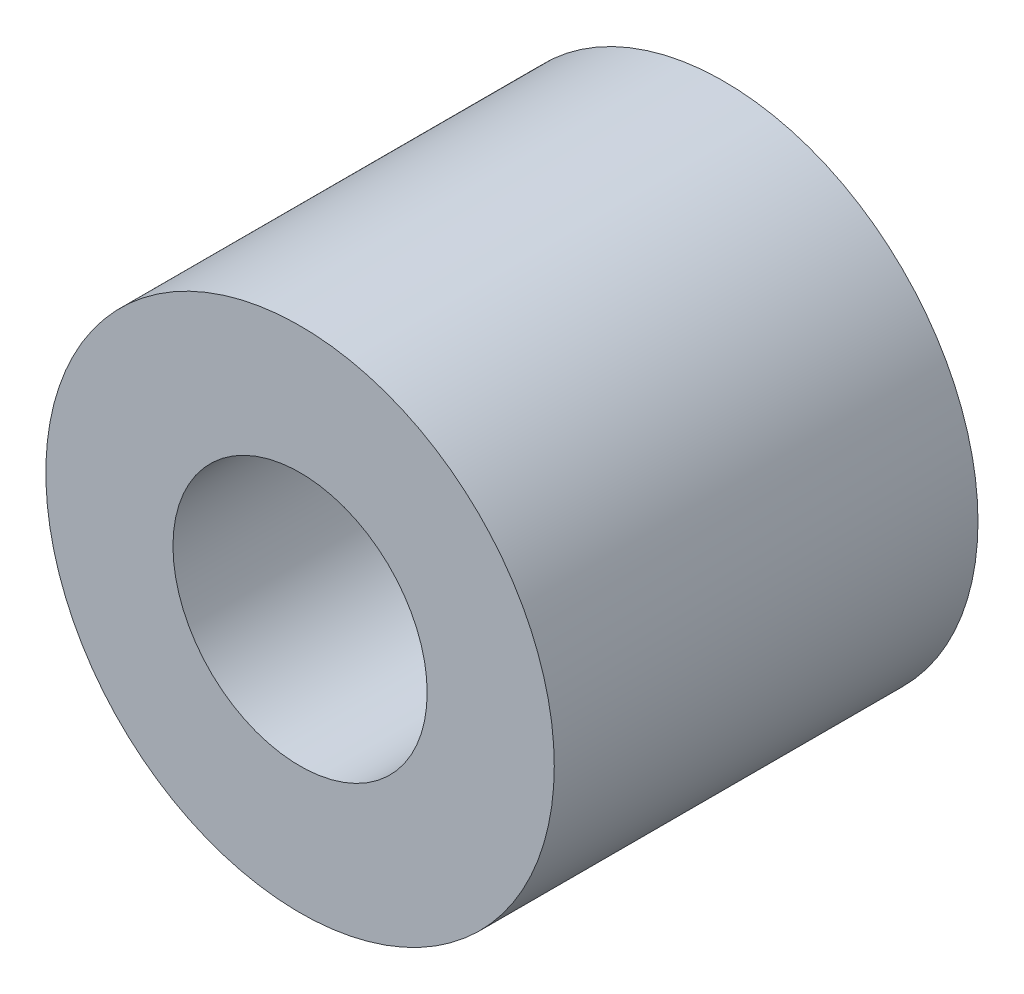
SolidWorks part; units mm, degrees
ref_plane "Front Plane" through (0, 0, 0) normal (0, 0, 1) x (1, 0, 0)
ref_plane "Top Plane" through (0, 0, 0) normal (0, 1, 0) x (1, 0, 0)
ref_plane "Right Plane" through (0, 0, 0) normal (1, 0, 0) x (0, 0, -1)
sketch "Sketch1" plane through (0, 0, 0) normal (0, 0, 1) x (1, 0, 0)
  circle A0 centre (0, 0) radius 3
  circle A1 centre (0, 0) radius 1.5
  dimension "D1" = 6
  dimension "D2" = 3
extrude "Extrude1" add sketch "Sketch1" along normal blind 5
